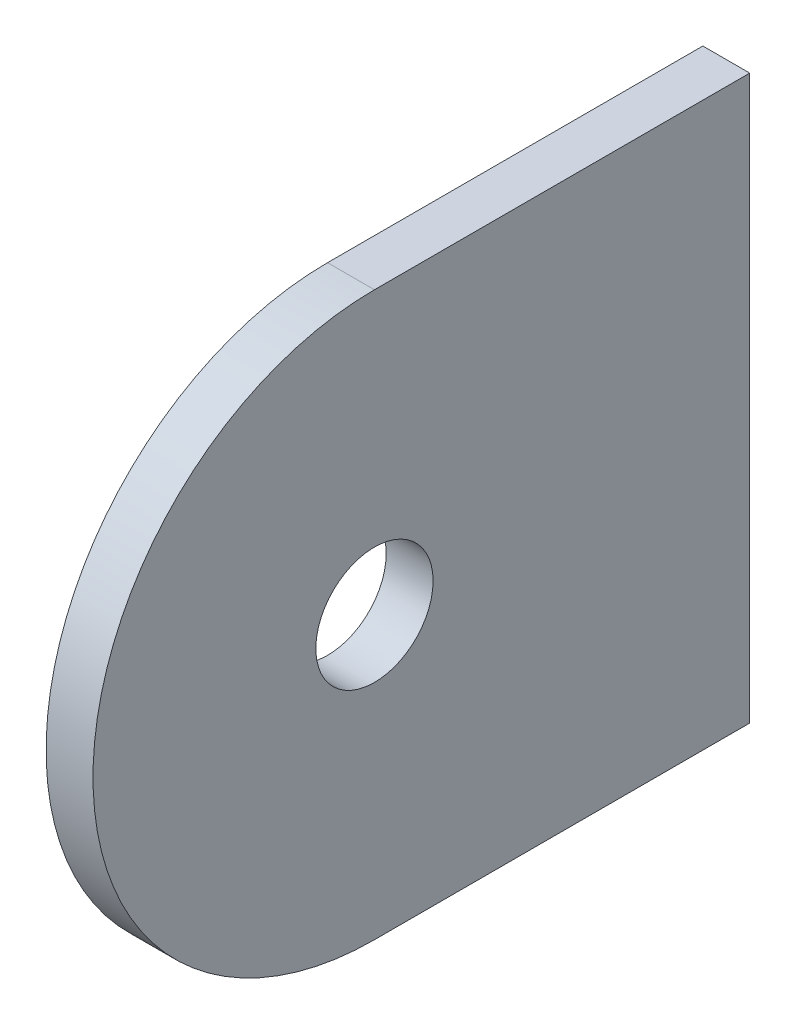
SolidWorks part; units mm, degrees
material "Plain Carbon Steel"
ref_plane "Front Plane" through (0, 0, 0) normal (0, 0, 1) x (1, 0, 0)
ref_plane "Top Plane" through (0, 0, 0) normal (0, 1, 0) x (1, 0, 0)
ref_plane "Right Plane" through (0, 0, 0) normal (1, 0, 0) x (0, 0, -1)
sketch "Sketch1" plane through (0, 0, 0) normal (1, 0, 0) x (0, 0, -1)
  line L0 (1.7463, 0) -> (-1.7463, 0) construction
  line L1 (-25.4, -19.05) -> (0, -19.05)
  line L2 (-25.4, -19.05) -> (-25.4, 19.05) construction
  line L3 (-25.4, 19.05) -> (0, 19.05)
  line L4 (0, -19.05) -> (0, 19.05)
  line L5 (-25.4, -19.05) -> (0, 19.05) construction
  line L6 (-25.4, 19.05) -> (0, -19.05) construction
  line L7 (0, 1.7463) -> (0, -1.7463) construction
  arc A0 (-25.4, 19.05) -> (-25.4, -19.05) centre (-25.4, 0) ccw
  circle A1 centre (-25.4, 0) radius 3.9688
  point P0 (-12.7, 0)
  dimension "D3" = 7.9375
  dimension "D1" = 25.4
  dimension "D2" = 38.1
extrude "Boss-Extrude1" add sketch "Sketch1" along normal mid plane 3.175
